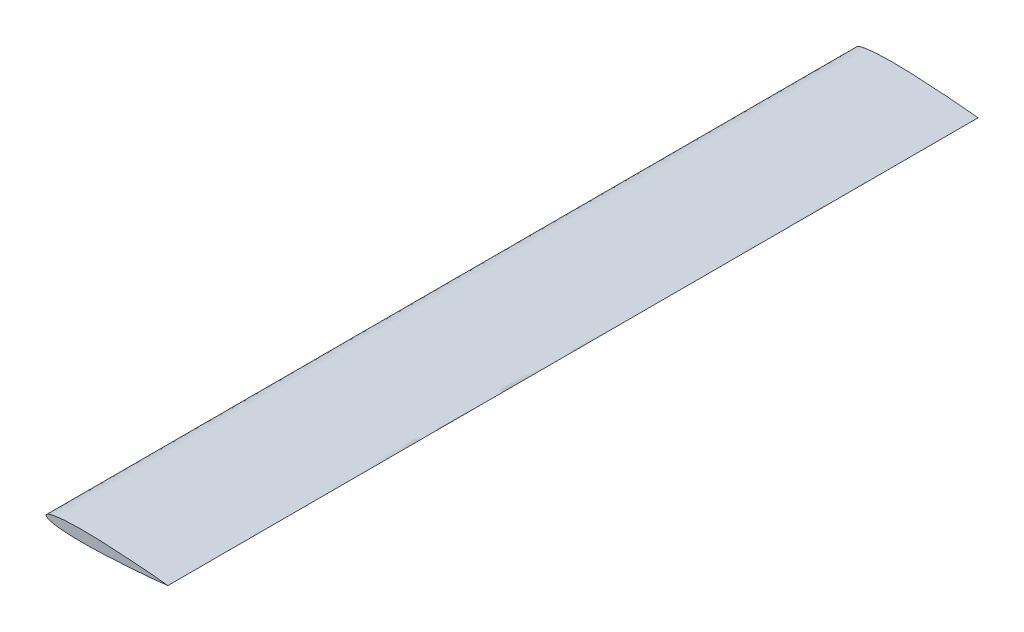
SolidWorks part; units mm, degrees
ref_plane "Front Plane" through (0, 0, 0) normal (0, 0, 1) x (1, 0, 0)
ref_plane "Top Plane" through (0, 0, 0) normal (0, 1, 0) x (1, 0, 0)
ref_plane "Right Plane" through (0, 0, 0) normal (1, 0, 0) x (0, 0, -1)
curve "Curve1"
  spline degree 3 poles (198.173, -0.1902, 0) (200.4592, 0, 0) (198.173, 0.1902, 0) (196.2993, 0.5074, 0) (191.7479, 0.9938, 0) (186.1558, 1.5974, 0) (178.8694, 2.3058, 0) (170.3147, 3.0876, 0) (160.5293, 3.9276, 0) (149.7178, 4.8013, 0) (138.0526, 5.6738, 0) (125.7371, 6.5193, 0) (112.9812, 7.2987, 0) (100.0033, 7.9792, 0) (87.0249, 8.5203, 0) (76.3087, 8.8329, 0) (67.9023, 8.9764, 0) (61.7868, 9.0274, 0) (55.8344, 9.0203, 0) (50.0707, 8.9437, 0) (44.5208, 8.8092, 0) (39.209, 8.606, 0) (34.1575, 8.3417, 0) (29.3873, 8.01, 0) (24.9186, 7.6164, 0) (20.772, 7.1577, 0) (16.9649, 6.6425, 0) (13.512, 6.0841, 0) (10.4279, 5.485, 0) (7.7224, 4.8473, 0) (5.4084, 4.1495, 0) (3.4909, 3.3786, 0) (1.9875, 2.5281, 0) (0.9063, 1.64, 0) (0.2312, 0.826, 0) (-0.0946, 0, 0) (0.2312, -0.826, 0) (0.9063, -1.64, 0) (1.9875, -2.5281, 0) (3.4909, -3.3786, 0) (5.4084, -4.1495, 0) (7.7224, -4.8473, 0) (10.4279, -5.485, 0) (13.512, -6.0841, 0) (16.9649, -6.6425, 0) (20.772, -7.1577, 0) (24.9186, -7.6164, 0) (29.3873, -8.01, 0) (34.1575, -8.3417, 0) (39.209, -8.606, 0) (44.5208, -8.8092, 0) (50.0707, -8.9437, 0) (55.8344, -9.0203, 0) (61.7868, -9.0274, 0) (67.9023, -8.9764, 0) (76.3087, -8.8329, 0) (87.0249, -8.5203, 0) (100.0033, -7.9792, 0) (112.9812, -7.2987, 0) (125.7371, -6.5193, 0) (138.0526, -5.6738, 0) (149.7178, -4.8013, 0) (160.5293, -3.9276, 0) (170.3147, -3.0876, 0) (178.8694, -2.3058, 0) (186.1558, -1.5974, 0) (191.7479, -0.9938, 0) (196.2993, -0.5074, 0) (198.173, -0.1902, 0) (200.4592, 0, 0) (198.173, 0.1902, 0) knots -0.018944 -0.008488 -0.002133 0 0.002133 0.008488 0.018944 0.033319 0.051356 0.072756 0.097141 0.124097 0.153163 0.183834 0.215589 0.247878 0.280151 0.31186 0.327333 0.342463 0.357187 0.371448 0.385183 0.398331 0.410845 0.422673 0.433769 0.44409 0.453589 0.46224 0.47001 0.476871 0.482833 0.487909 0.492155 0.495592 0.498196 0.5 0.501804 0.504408 0.507845 0.512091 0.517167 0.523129 0.52999 0.53776 0.546411 0.55591 0.566231 0.577327 0.589155 0.601669 0.614817 0.628552 0.642813 0.657537 0.672667 0.68814 0.719849 0.752122 0.784411 0.816166 0.846837 0.875903 0.902859 0.927244 0.948644 0.966681 0.981056 0.991512 0.997867 1 1.002133 1.008488 1.018944 periodic
sketch "Sketch1" plane through (0, 0, 0) normal (0, 0, 1) x (1, 0, 0)
  spline S0 degree 3 poles (198.173, -0.1902) (200.4592, 0) (198.173, 0.1902) (196.2993, 0.5074) (191.7479, 0.9938) (186.1558, 1.5974) (178.8694, 2.3058) (170.3147, 3.0876) (160.5293, 3.9276) (149.7178, 4.8013) (138.0526, 5.6738) (125.7371, 6.5193) (112.9812, 7.2987) (100.0033, 7.9792) (87.0249, 8.5203) (76.3087, 8.8329) (67.9023, 8.9764) (61.7868, 9.0274) (55.8344, 9.0203) (50.0707, 8.9437) (44.5208, 8.8092) (39.209, 8.606) (34.1575, 8.3417) (29.3873, 8.01) (24.9186, 7.6164) (20.772, 7.1577) (16.9649, 6.6425) (13.512, 6.0841) (10.4279, 5.485) (7.7224, 4.8473) (5.4084, 4.1495) (3.4909, 3.3786) (1.9875, 2.5281) (0.9063, 1.64) (0.2312, 0.826) (-0.0946, 0) (0.2312, -0.826) (0.9063, -1.64) (1.9875, -2.5281) (3.4909, -3.3786) (5.4084, -4.1495) (7.7224, -4.8473) (10.4279, -5.485) (13.512, -6.0841) (16.9649, -6.6425) (20.772, -7.1577) (24.9186, -7.6164) (29.3873, -8.01) (34.1575, -8.3417) (39.209, -8.606) (44.5208, -8.8092) (50.0707, -8.9437) (55.8344, -9.0203) (61.7868, -9.0274) (67.9023, -8.9764) (76.3087, -8.8329) (87.0249, -8.5203) (100.0033, -7.9792) (112.9812, -7.2987) (125.7371, -6.5193) (138.0526, -5.6738) (149.7178, -4.8013) (160.5293, -3.9276) (170.3147, -3.0876) (178.8694, -2.3058) (186.1558, -1.5974) (191.7479, -0.9938) (196.2993, -0.5074) (198.173, -0.1902) (200.4592, 0) (198.173, 0.1902) knots -0.018944 -0.008488 -0.002133 0 0.002133 0.008488 0.018944 0.033319 0.051356 0.072756 0.097141 0.124097 0.153163 0.183834 0.215589 0.247878 0.280151 0.31186 0.327333 0.342463 0.357187 0.371448 0.385183 0.398331 0.410845 0.422673 0.433769 0.44409 0.453589 0.46224 0.47001 0.476871 0.482833 0.487909 0.492155 0.495592 0.498196 0.5 0.501804 0.504408 0.507845 0.512091 0.517167 0.523129 0.52999 0.53776 0.546411 0.55591 0.566231 0.577327 0.589155 0.601669 0.614817 0.628552 0.642813 0.657537 0.672667 0.68814 0.719849 0.752122 0.784411 0.816166 0.846837 0.875903 0.902859 0.927244 0.948644 0.966681 0.981056 0.991512 0.997867 1 1.002133 1.008488 1.018944 only from (200, 0) to (200, 0) construction
  spline S1 degree 3 poles (198.173, -0.1902) (200.4592, 0) (198.173, 0.1902) (196.2993, 0.5074) (191.7479, 0.9938) (186.1558, 1.5974) (178.8694, 2.3058) (170.3147, 3.0876) (160.5293, 3.9276) (149.7178, 4.8013) (138.0526, 5.6738) (125.7371, 6.5193) (112.9812, 7.2987) (100.0033, 7.9792) (87.0249, 8.5203) (76.3087, 8.8329) (67.9023, 8.9764) (61.7868, 9.0274) (55.8344, 9.0203) (50.0707, 8.9437) (44.5208, 8.8092) (39.209, 8.606) (34.1575, 8.3417) (29.3873, 8.01) (24.9186, 7.6164) (20.772, 7.1577) (16.9649, 6.6425) (13.512, 6.0841) (10.4279, 5.485) (7.7224, 4.8473) (5.4084, 4.1495) (3.4909, 3.3786) (1.9875, 2.5281) (0.9063, 1.64) (0.2312, 0.826) (-0.0946, 0) (0.2312, -0.826) (0.9063, -1.64) (1.9875, -2.5281) (3.4909, -3.3786) (5.4084, -4.1495) (7.7224, -4.8473) (10.4279, -5.485) (13.512, -6.0841) (16.9649, -6.6425) (20.772, -7.1577) (24.9186, -7.6164) (29.3873, -8.01) (34.1575, -8.3417) (39.209, -8.606) (44.5208, -8.8092) (50.0707, -8.9437) (55.8344, -9.0203) (61.7868, -9.0274) (67.9023, -8.9764) (76.3087, -8.8329) (87.0249, -8.5203) (100.0033, -7.9792) (112.9812, -7.2987) (125.7371, -6.5193) (138.0526, -5.6738) (149.7178, -4.8013) (160.5293, -3.9276) (170.3147, -3.0876) (178.8694, -2.3058) (186.1558, -1.5974) (191.7479, -0.9938) (196.2993, -0.5074) (198.173, -0.1902) (200.4592, 0) (198.173, 0.1902) knots -0.018944 -0.008488 -0.002133 0 0.002133 0.008488 0.018944 0.033319 0.051356 0.072756 0.097141 0.124097 0.153163 0.183834 0.215589 0.247878 0.280151 0.31186 0.327333 0.342463 0.357187 0.371448 0.385183 0.398331 0.410845 0.422673 0.433769 0.44409 0.453589 0.46224 0.47001 0.476871 0.482833 0.487909 0.492155 0.495592 0.498196 0.5 0.501804 0.504408 0.507845 0.512091 0.517167 0.523129 0.52999 0.53776 0.546411 0.55591 0.566231 0.577327 0.589155 0.601669 0.614817 0.628552 0.642813 0.657537 0.672667 0.68814 0.719849 0.752122 0.784411 0.816166 0.846837 0.875903 0.902859 0.927244 0.948644 0.966681 0.981056 0.991512 0.997867 1 1.002133 1.008488 1.018944 only from (200, 0) to (200, 0)
extrude "Boss-Extrude1" add sketch "Sketch1" along normal blind 1330
sketch "Sketch2" plane through (0, 0, 1330) normal (0, 0, 1) x (1, 0, 0)
  line L0 (0, 0) -> (200, 0) construction
  spline S0 degree 3 poles (198.173, -0.1902) (200.4592, 0) (198.173, 0.1902) (196.2993, 0.5074) (191.7479, 0.9938) (186.1558, 1.5974) (178.8694, 2.3058) (170.3147, 3.0876) (160.5293, 3.9276) (149.7178, 4.8013) (138.0526, 5.6738) (125.7371, 6.5193) (112.9812, 7.2987) (100.0033, 7.9792) (87.0249, 8.5203) (76.3087, 8.8329) (67.9023, 8.9764) (61.7868, 9.0274) (55.8344, 9.0203) (50.0707, 8.9437) (44.5208, 8.8092) (39.209, 8.606) (34.1575, 8.3417) (29.3873, 8.01) (24.9186, 7.6164) (20.772, 7.1577) (16.9649, 6.6425) (13.512, 6.0841) (10.4279, 5.485) (7.7224, 4.8473) (5.4084, 4.1495) (3.4909, 3.3786) (1.9875, 2.5281) (0.9063, 1.64) (0.2312, 0.826) (-0.0946, 0) (0.2312, -0.826) (0.9063, -1.64) (1.9875, -2.5281) (3.4909, -3.3786) (5.4084, -4.1495) (7.7224, -4.8473) (10.4279, -5.485) (13.512, -6.0841) (16.9649, -6.6425) (20.772, -7.1577) (24.9186, -7.6164) (29.3873, -8.01) (34.1575, -8.3417) (39.209, -8.606) (44.5208, -8.8092) (50.0707, -8.9437) (55.8344, -9.0203) (61.7868, -9.0274) (67.9023, -8.9764) (76.3087, -8.8329) (87.0249, -8.5203) (100.0033, -7.9792) (112.9812, -7.2987) (125.7371, -6.5193) (138.0526, -5.6738) (149.7178, -4.8013) (160.5293, -3.9276) (170.3147, -3.0876) (178.8694, -2.3058) (186.1558, -1.5974) (191.7479, -0.9938) (196.2993, -0.5074) (198.173, -0.1902) (200.4592, 0) (198.173, 0.1902) knots -0.018944 -0.008488 -0.002133 0 0.002133 0.008488 0.018944 0.033319 0.051356 0.072756 0.097141 0.124097 0.153163 0.183834 0.215589 0.247878 0.280151 0.31186 0.327333 0.342463 0.357187 0.371448 0.385183 0.398331 0.410845 0.422673 0.433769 0.44409 0.453589 0.46224 0.47001 0.476871 0.482833 0.487909 0.492155 0.495592 0.498196 0.5 0.501804 0.504408 0.507845 0.512091 0.517167 0.523129 0.52999 0.53776 0.546411 0.55591 0.566231 0.577327 0.589155 0.601669 0.614817 0.628552 0.642813 0.657537 0.672667 0.68814 0.719849 0.752122 0.784411 0.816166 0.846837 0.875903 0.902859 0.927244 0.948644 0.966681 0.981056 0.991512 0.997867 1 1.002133 1.008488 1.018944 only from (200, 0) to (200, 0) construction
